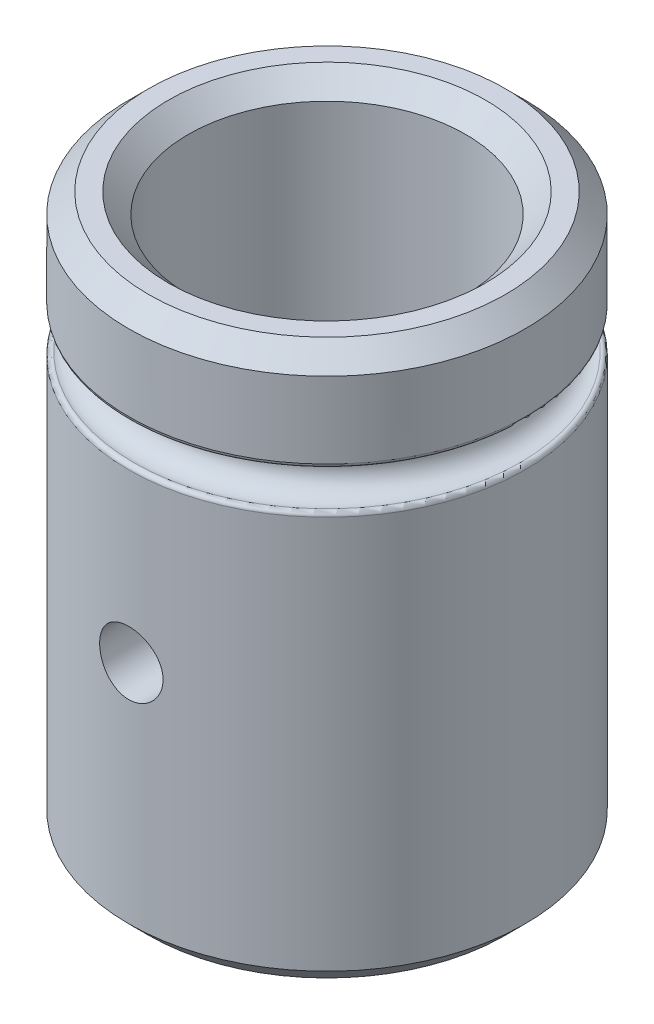
SolidWorks part; units mm, degrees
ref_plane "Front Plane" through (0, 0, 0) normal (0, 0, 1) x (1, 0, 0)
ref_plane "Top Plane" through (0, 0, 0) normal (0, 1, 0) x (1, 0, 0)
ref_plane "Right Plane" through (0, 0, 0) normal (1, 0, 0) x (0, 0, -1)
sketch "Sketch1" plane through (0, 0, 0) normal (0, 1, 0) x (1, 0, 0)
  circle A0 centre (0, 0) radius 3.5
  circle A2 centre (0, 0) radius 5
  dimension "D1" = 7
  dimension "D2" = 10
extrude "Boss-Extrude1" add sketch "Sketch1" along normal blind 14
sketch "Sketch3" plane through (0, 0, 0) normal (0, 0, 1) x (1, 0, 0)
  circle A0 centre (0, 6.2) radius 0.8
  point P4 (0, 7)
  dimension "D1" = 1.6
  dimension "D2" = 7
extrude "Cut-Extrude1" cut sketch "Sketch3" along normal through all
sketch "Sketch4" plane through (0, 0, 0) normal (0, 0, 1) x (1, 0, 0)
  line L0 (0, 0) -> (0, 14) construction
  line L1 (3.5, 14) -> (-3.5, 14) construction
  line L2 (5, 14) -> (-5, 14) construction
  circle A0 centre (4.75, 11) radius 0.5
  point P7 (4.25, 11)
  point P8 (5.25, 11)
  dimension "D1" = 1
  dimension "D2" = 8.5
  dimension "D3" = 3
revolve "Cut-Revolve1" cut sketch "Sketch4" angle 360 about L0
fillet "Fillet1" radius 0.1 2 edges at (0, 11.433, -5) (0, 10.567, 5)
chamfer "Chamfer1" distance 0.5 angle 45 4 edges at (0, 14, 3.5) (0, 0, 3.5) (0, 0, 5) (0, 14, 5)
